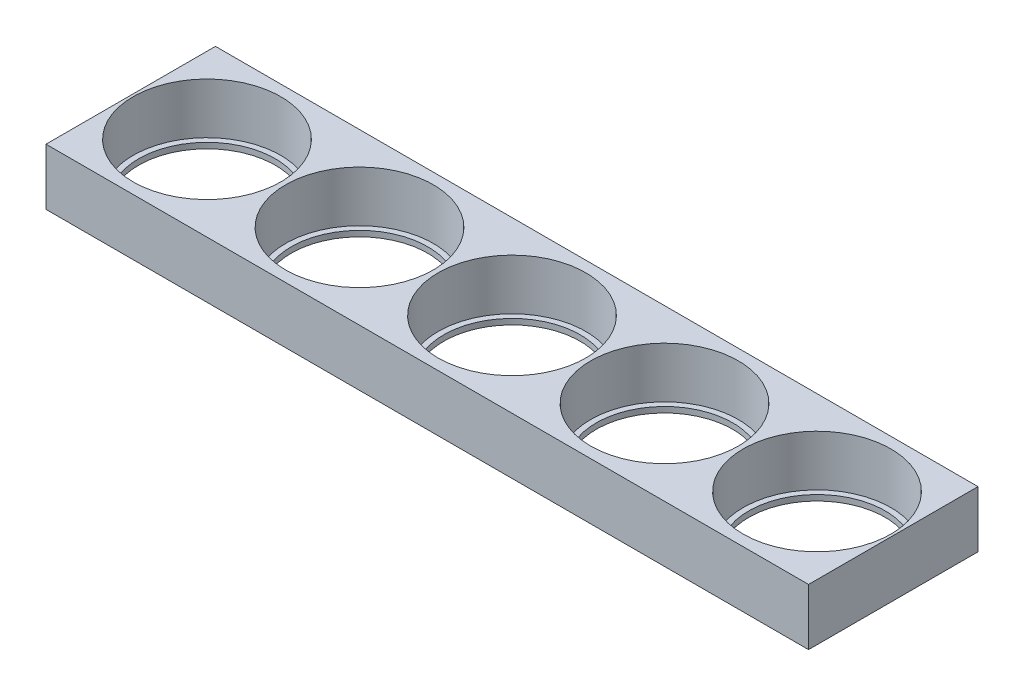
SolidWorks part; units mm, degrees
ref_plane "Plan de face" through (0, 0, 0) normal (0, 0, 1) x (1, 0, 0)
ref_plane "Plan de dessus" through (0, 0, 0) normal (0, 1, 0) x (1, 0, 0)
ref_plane "Plan de droite" through (0, 0, 0) normal (1, 0, 0) x (0, 0, -1)
sketch "Esquisse1" plane through (0, 0, 0) normal (0, 1, 0) x (1, 0, 0)
  line L5 (-13.5, -15) -> (13.5, -15)
  line L19 (-13.5, -15) -> (-13.5, 15)
  line L20 (-13.5, 15) -> (13.5, 15)
  line L21 (13.5, -15) -> (13.5, 15)
  line L22 (-13.5, -15) -> (13.5, 15) construction
  line L23 (-13.5, 15) -> (13.5, -15) construction
  circle A6 centre (0, 0) radius 13.075
  dimension "D2" = 15
  dimension "D3" = 13.5
  dimension "D1" = 26.15
extrude "Boss.-Extru.1" add sketch "Esquisse1" along normal blind 10
sketch "Esquisse4" plane through (0, 0, 0) normal (0, 1, 0) x (1, 0, 0)
  circle A0 centre (0, 0) radius 13.075 construction
  circle A1 centre (0, 0) radius 13.075
  circle A2 centre (0, 0) radius 12.075
  dimension "D1" = 1
extrude "Boss.-Extru.2" add sketch "Esquisse4" along normal blind 1
pattern_linear "Répétition linéaire1" count 3 spacing 27 along (1, 0, 0) count 3 spacing 27 along (-1, 0, 0) of "Boss.-Extru.1", "Boss.-Extru.2"
